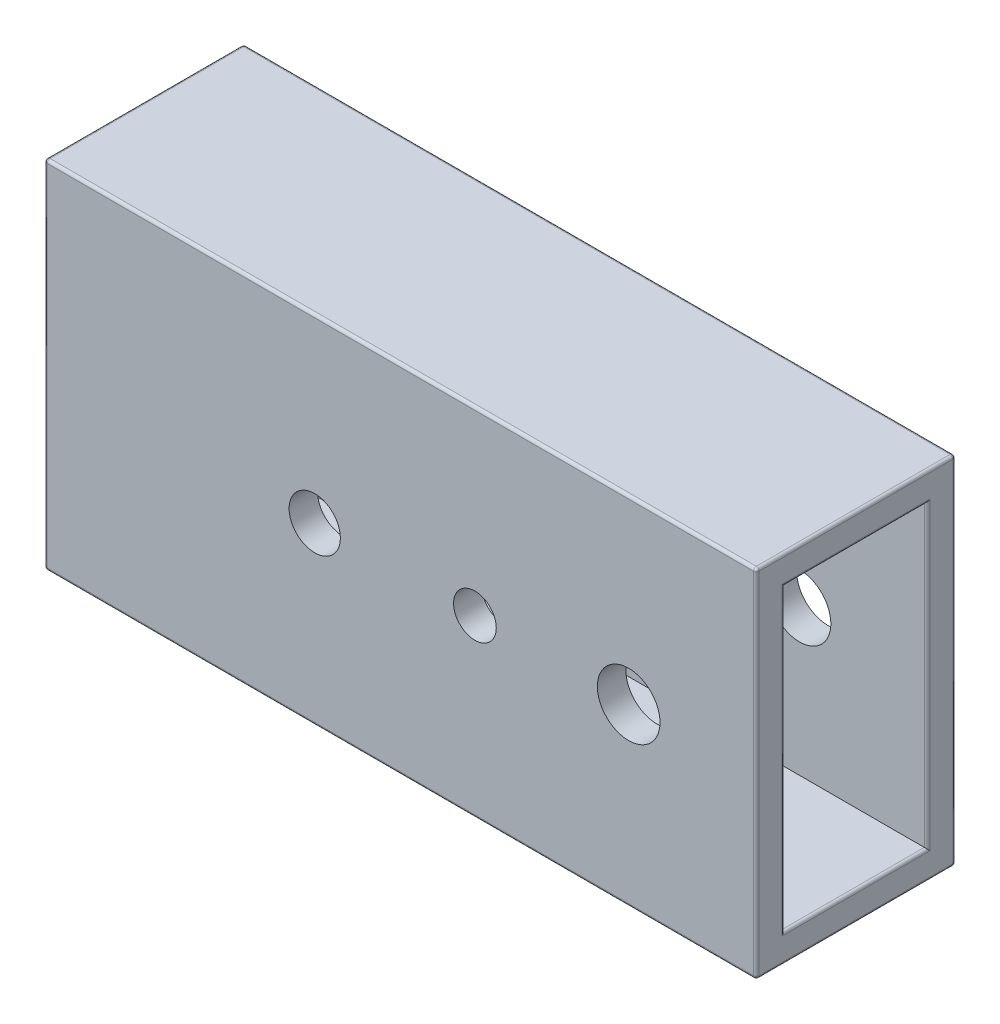
SolidWorks part; units mm, degrees
ref_plane "Front Plane" through (0, 0, 0) normal (0, 0, 1) x (1, 0, 0)
ref_plane "Top Plane" through (0, 0, 0) normal (0, 1, 0) x (1, 0, 0)
ref_plane "Right Plane" through (0, 0, 0) normal (1, 0, 0) x (0, 0, -1)
sketch "Sketch1" plane through (0, 0, 0) normal (0, 0, 1) x (1, 0, 0)
  line L1 (-255.1883, 93.431) -> (-5.1883, 93.431)
  line L2 (-255.1883, 93.431) -> (-255.1883, -31.569)
  line L3 (-255.1883, -31.569) -> (-5.1883, -31.569)
  line L4 (-5.1883, 93.431) -> (-5.1883, -31.569)
  line L5 (-255.1883, 93.431) -> (-5.1883, -31.569) construction
  line L6 (-255.1883, -31.569) -> (-5.1883, 93.431) construction
  point P0 (-130.1883, 30.931)
  dimension "D1" = 125
  dimension "D2" = 250
extrude "Boss-Extrude1" add sketch "Sketch1" along normal mid plane 70
shell "Shell1" thickness 10
sketch "Sketch2" plane through (0, 0, 35) normal (0, 0, 1) x (1, 0, 0)
  circle A0 centre (-50, 30) radius 11
  circle A1 centre (-104, 30) radius 7.5
  circle A2 centre (-160.25, 30) radius 9
  dimension "D2" = 15
  dimension "D3" = 18
extrude "Cut-Extrude1" cut sketch "Sketch2" against normal blind 70
fillet "Fillet1" radius 1 16 edges at (-130.1883, -31.569, 35) (-130.1883, -31.569, -35) (-5.1883, 83.431, 0) (-5.1883, 30.931, 25) (-5.1883, -21.569, 0) (-5.1883, 30.931, -25) (-5.1883, -31.569, 0) (-5.1883, 30.931, 35) (-5.1883, 30.931, -35) (-255.1883, 30.931, 35) (-255.1883, -31.569, 0) (-255.1883, 30.931, -35) (-5.1883, 93.431, 0) (-130.1883, 93.431, 35) (-255.1883, 93.431, 0) (-130.1883, 93.431, -35)
